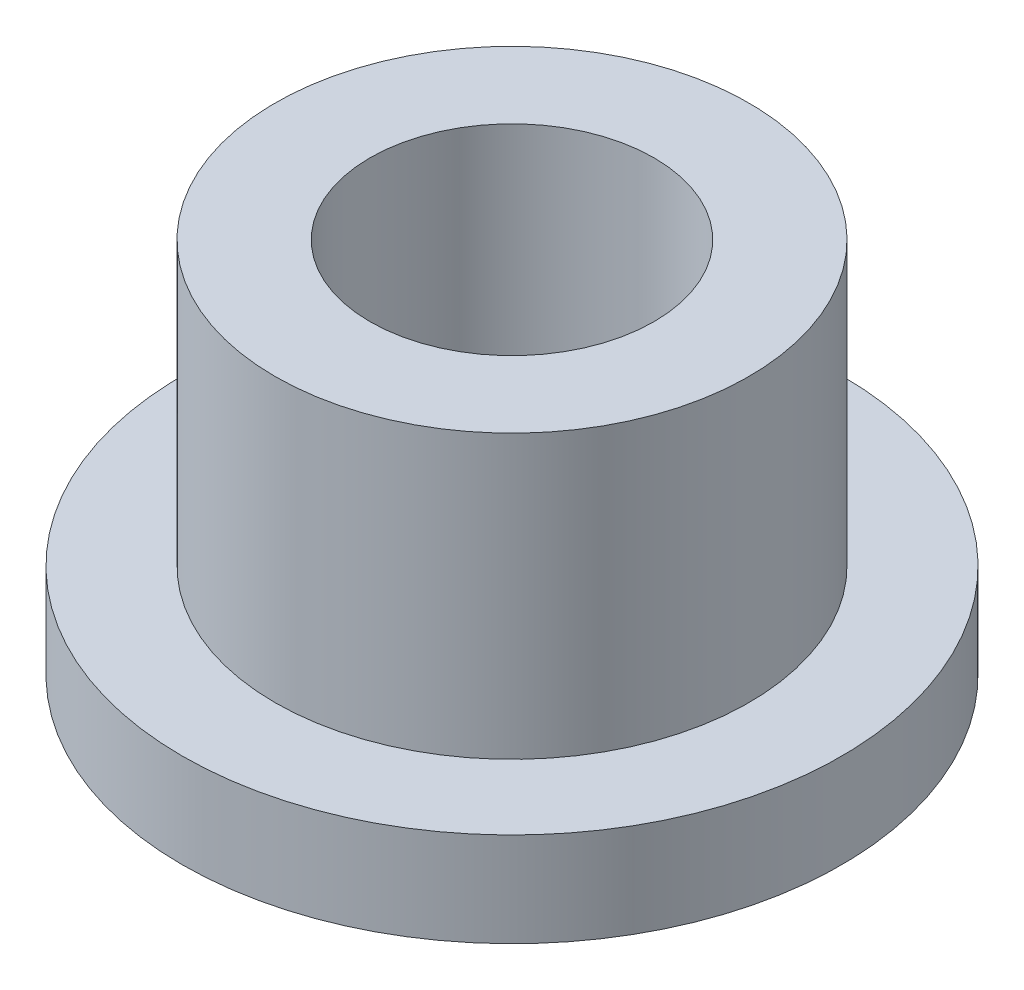
SolidWorks part; units mm, degrees
material "Commercial Bronze, UNS C22000 (90-10 Bronze)"
ref_plane "Front" through (0, 0, 0) normal (0, 0, 1) x (1, 0, 0)
ref_plane "Top" through (0, 0, 0) normal (0, 1, 0) x (1, 0, 0)
ref_plane "Right" through (0, 0, 0) normal (1, 0, 0) x (0, 0, -1)
sketch "Sketch1" plane through (0, 0, 0) normal (0, 1, 0) x (1, 0, 0)
  circle A0 centre (0, 0) radius 2.394
  circle A1 centre (0, 0) radius 3.9942
  circle A2 centre (0, 0) radius 5.5563
  dimension "ID" = 4.7879
  dimension "OD" = 7.9883
  dimension "FlangeOD" = 11.1125
sketch "Sketch2" plane through (0, 0, 0) normal (0, 1, 0) x (1, 0, 0)
  circle A0 centre (0, 0) radius 2.394 construction
  circle A1 centre (0, 0) radius 3.9942 construction
  circle A2 centre (0, 0) radius 2.394
  circle A3 centre (0, 0) radius 3.9942
extrude "Boss-Extrude1" add sketch "Sketch2" along normal blind 6.35
sketch "Sketch3" plane through (0, 0, 0) normal (0, 1, 0) x (1, 0, 0)
  circle A0 centre (0, 0) radius 5.5563 construction
  circle A1 centre (0, 0) radius 3.9942 construction
  circle A2 centre (0, 0) radius 5.5563
  circle A3 centre (0, 0) radius 3.9942
extrude "Boss-Extrude2" add sketch "Sketch3" along normal blind 1.5875
